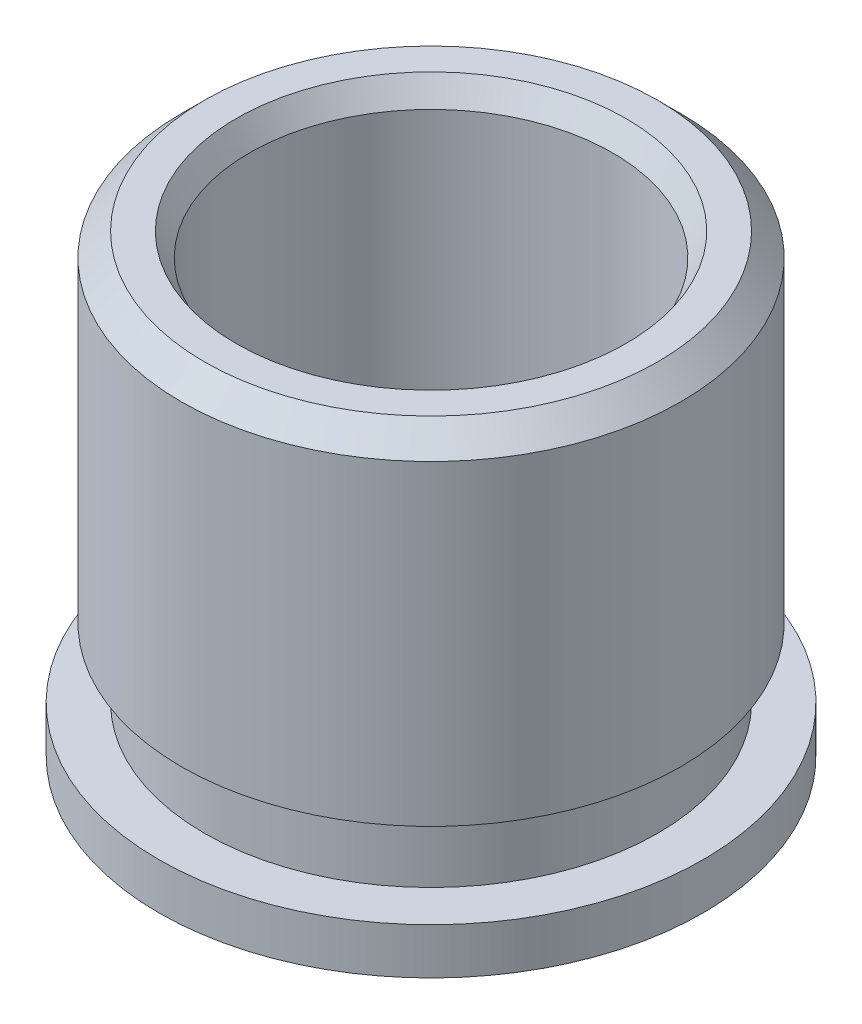
SolidWorks part; units mm, degrees
material "Brass"
ref_plane "Front Plane" through (0, 0, 0) normal (0, 0, 1) x (1, 0, 0)
ref_plane "Top Plane" through (0, 0, 0) normal (0, 1, 0) x (1, 0, 0)
ref_plane "Right Plane" through (0, 0, 0) normal (1, 0, 0) x (0, 0, -1)
sketch "Sketch1" plane through (0, 0, 0) normal (0, 0, 1) x (1, 0, 0)
  line L0 (0, 2.5019) -> (0, -2.5019)
  line L1 (2.1466, -2.5019) -> (2.9972, -2.5019)
  line L2 (2.1466, -2.5019) -> (2, -2.2479)
  line L3 (2, -2.2479) -> (2, 2.2479)
  line L4 (2, 2.2479) -> (2.1466, 2.5019)
  line L5 (2.1466, 2.5019) -> (2.4956, 2.5019)
  line L6 (2.4956, 2.5019) -> (2.7495, 2.2479)
  line L7 (2.7495, 2.2479) -> (2.7495, -1.2319)
  line L8 (2.7495, -1.2319) -> (2.4956, -1.2319)
  line L9 (2.4956, -1.2319) -> (2.4956, -1.9939)
  line L10 (2.4956, -1.9939) -> (2.9972, -1.9939)
  line L11 (2.9972, -1.9939) -> (2.9972, -2.5019)
  dimension "D1" = 5.0038
  dimension "D2" = 2
  dimension "D3" = 0.254
  dimension "D4" = 30
  dimension "D5" = 0.254
  dimension "D6" = 0.254
  dimension "D7" = 0.254
  dimension "D8" = 2.7495
  dimension "D9" = 2.9972
  dimension "D10" = 0.254
  dimension "D11" = 0.762
  dimension "D12" = 0.508
revolve "Revolve1" add sketch "Sketch1" angle 360 about L0
